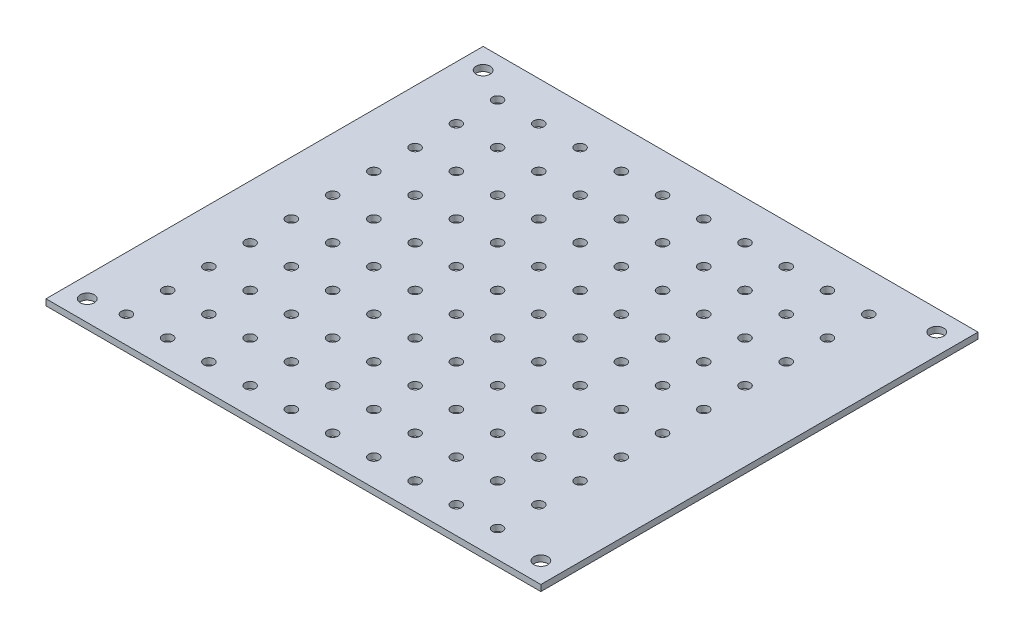
SolidWorks part; units mm, degrees
ref_plane "Front Plane" through (0, 0, 0) normal (0, 0, 1) x (1, 0, 0)
ref_plane "Top Plane" through (0, 0, 0) normal (0, 1, 0) x (1, 0, 0)
ref_plane "Right Plane" through (0, 0, 0) normal (1, 0, 0) x (0, 0, -1)
sketch "Sketch1" plane through (0, 0, 0) normal (0, 1, 0) x (1, 0, 0)
  line L0 (115, 101) -> (5, 101) construction
  line L1 (0, 0) -> (120, 0)
  line L2 (0, 0) -> (0, 106)
  line L3 (0, 106) -> (120, 106)
  line L4 (120, 0) -> (120, 106)
  line L6 (115, 101) -> (115, 5) construction
  circle A17 centre (13, 36.5) radius 1.25
  circle A18 centre (23, 36.5) radius 1.25
  circle A19 centre (13, 6.5) radius 1.25
  circle A28 centre (5, 5) radius 1.7
  circle A29 centre (5, 101) radius 1.7
  circle A30 centre (115, 101) radius 1.7
  circle A31 centre (115, 5) radius 1.7
  circle A32 centre (23, 6.5) radius 1.25
  circle A33 centre (33, 6.5) radius 1.25
  circle A34 centre (23, 16.5) radius 1.25
  circle A35 centre (33, 16.5) radius 1.25
  circle A36 centre (23, 26.5) radius 1.25
  circle A37 centre (33, 26.5) radius 1.25
  circle A38 centre (13, 16.5) radius 1.25
  circle A39 centre (13, 26.5) radius 1.25
  circle A40 centre (33, 36.5) radius 1.25
  circle A41 centre (13, 46.5) radius 1.25
  circle A42 centre (23, 46.5) radius 1.25
  circle A43 centre (33, 46.5) radius 1.25
  circle A44 centre (13, 56.5) radius 1.25
  circle A45 centre (23, 56.5) radius 1.25
  circle A46 centre (33, 56.5) radius 1.25
  circle A47 centre (13, 66.5) radius 1.25
  circle A48 centre (23, 66.5) radius 1.25
  circle A49 centre (33, 66.5) radius 1.25
  circle A50 centre (13, 76.5) radius 1.25
  circle A51 centre (23, 76.5) radius 1.25
  circle A52 centre (33, 76.5) radius 1.25
  circle A53 centre (13, 86.5) radius 1.25
  circle A54 centre (23, 86.5) radius 1.25
  circle A55 centre (33, 86.5) radius 1.25
  circle A56 centre (13, 96.5) radius 1.25
  circle A57 centre (23, 96.5) radius 1.25
  circle A58 centre (33, 96.5) radius 1.25
  circle A59 centre (43, 6.5) radius 1.25
  circle A60 centre (53, 6.5) radius 1.25
  circle A61 centre (63, 6.5) radius 1.25
  circle A62 centre (73, 6.5) radius 1.25
  circle A63 centre (83, 6.5) radius 1.25
  circle A64 centre (93, 6.5) radius 1.25
  circle A65 centre (103, 6.5) radius 1.25
  circle A66 centre (43, 16.5) radius 1.25
  circle A67 centre (53, 16.5) radius 1.25
  circle A68 centre (63, 16.5) radius 1.25
  circle A69 centre (73, 16.5) radius 1.25
  circle A70 centre (83, 16.5) radius 1.25
  circle A71 centre (93, 16.5) radius 1.25
  circle A72 centre (103, 16.5) radius 1.25
  circle A73 centre (43, 26.5) radius 1.25
  circle A74 centre (53, 26.5) radius 1.25
  circle A75 centre (63, 26.5) radius 1.25
  circle A76 centre (73, 26.5) radius 1.25
  circle A77 centre (83, 26.5) radius 1.25
  circle A78 centre (93, 26.5) radius 1.25
  circle A79 centre (103, 26.5) radius 1.25
  circle A80 centre (43, 36.5) radius 1.25
  circle A81 centre (53, 36.5) radius 1.25
  circle A82 centre (63, 36.5) radius 1.25
  circle A83 centre (73, 36.5) radius 1.25
  circle A84 centre (83, 36.5) radius 1.25
  circle A85 centre (93, 36.5) radius 1.25
  circle A86 centre (103, 36.5) radius 1.25
  circle A87 centre (43, 46.5) radius 1.25
  circle A88 centre (53, 46.5) radius 1.25
  circle A89 centre (63, 46.5) radius 1.25
  circle A90 centre (73, 46.5) radius 1.25
  circle A91 centre (83, 46.5) radius 1.25
  circle A92 centre (93, 46.5) radius 1.25
  circle A93 centre (103, 46.5) radius 1.25
  circle A94 centre (43, 56.5) radius 1.25
  circle A95 centre (53, 56.5) radius 1.25
  circle A96 centre (63, 56.5) radius 1.25
  circle A97 centre (73, 56.5) radius 1.25
  circle A98 centre (83, 56.5) radius 1.25
  circle A99 centre (93, 56.5) radius 1.25
  circle A100 centre (103, 56.5) radius 1.25
  circle A101 centre (43, 66.5) radius 1.25
  circle A102 centre (53, 66.5) radius 1.25
  circle A103 centre (63, 66.5) radius 1.25
  circle A104 centre (73, 66.5) radius 1.25
  circle A105 centre (83, 66.5) radius 1.25
  circle A106 centre (93, 66.5) radius 1.25
  circle A107 centre (103, 66.5) radius 1.25
  circle A108 centre (43, 76.5) radius 1.25
  circle A109 centre (53, 76.5) radius 1.25
  circle A110 centre (63, 76.5) radius 1.25
  circle A111 centre (73, 76.5) radius 1.25
  circle A112 centre (83, 76.5) radius 1.25
  circle A113 centre (93, 76.5) radius 1.25
  circle A114 centre (103, 76.5) radius 1.25
  circle A115 centre (43, 86.5) radius 1.25
  circle A116 centre (53, 86.5) radius 1.25
  circle A117 centre (63, 86.5) radius 1.25
  circle A118 centre (73, 86.5) radius 1.25
  circle A119 centre (83, 86.5) radius 1.25
  circle A120 centre (93, 86.5) radius 1.25
  circle A121 centre (103, 86.5) radius 1.25
  circle A122 centre (43, 96.5) radius 1.25
  circle A123 centre (53, 96.5) radius 1.25
  circle A124 centre (63, 96.5) radius 1.25
  circle A125 centre (73, 96.5) radius 1.25
  circle A126 centre (83, 96.5) radius 1.25
  circle A127 centre (93, 96.5) radius 1.25
  circle A128 centre (103, 96.5) radius 1.25
  point P7 (115, 53)
  point P9 (60, 101)
  point P10 (60, 106)
  point P20 (120, 53)
  dimension "D5" = 110
  dimension "D6" = 96
  dimension "D3" = 2.5
  dimension "D8" = 3.4
  dimension "D1" = 120
  dimension "D2" = 106
  dimension "D4" = 8
  dimension "D7" = 1.5
  dimension "D9" = 10
  dimension "D10" = 10
extrude "Boss-Extrude1" add sketch "Sketch1" along normal blind 1.5
equation "\"o\"= 10mm"
equation "\"P\"= 10"
